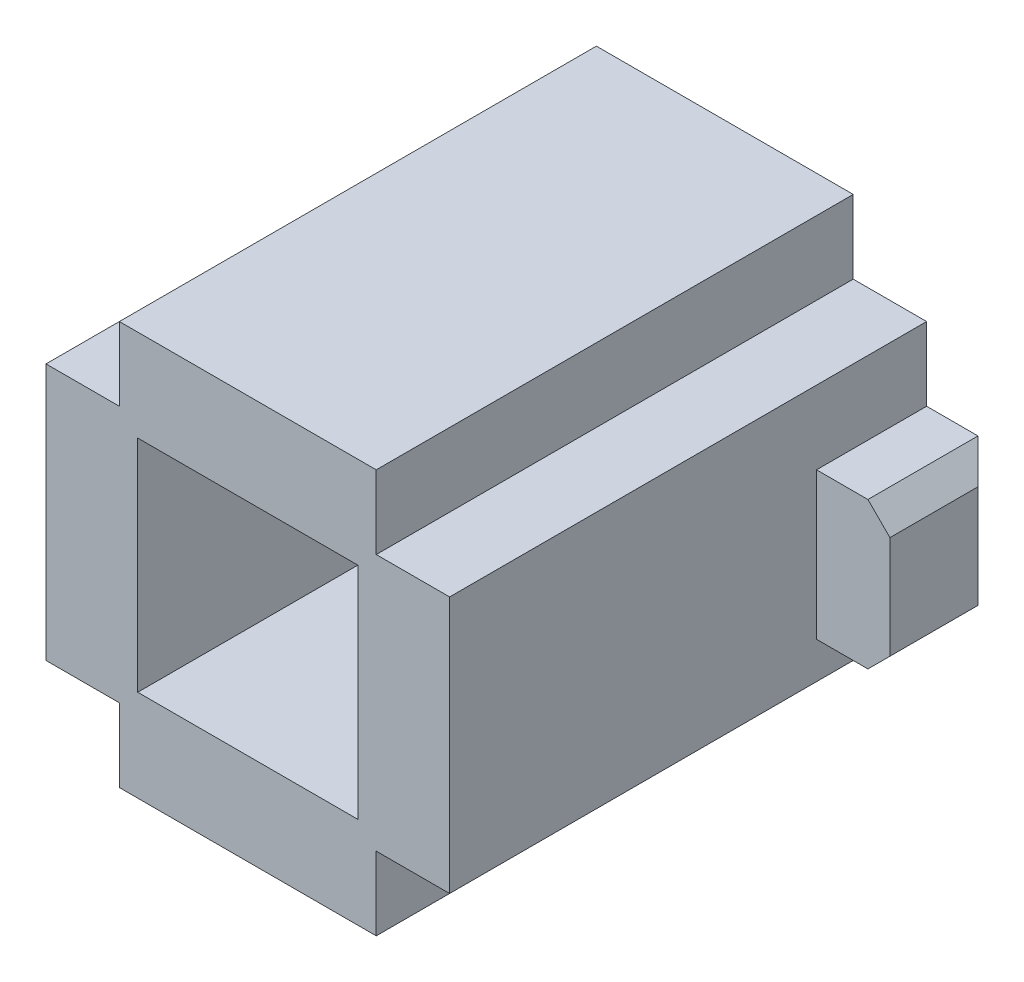
SolidWorks part; units mm, degrees
ref_plane "Front Plane" through (0, 0, 0) normal (0, 0, 1) x (1, 0, 0)
ref_plane "Top Plane" through (0, 0, 0) normal (0, 1, 0) x (1, 0, 0)
ref_plane "Right Plane" through (0, 0, 0) normal (1, 0, 0) x (0, 0, -1)
sketch "Sketch1" plane through (0, 0, 0) normal (0, 0, 1) x (1, 0, 0)
  line L0 (-17.5, 27.5) -> (-17.5, 17.5) construction
  line L1 (-17.5, 27.5) -> (17.5, 27.5)
  line L2 (-27.5, 17.5) -> (-27.5, -17.5)
  line L3 (-17.5, -27.5) -> (17.5, -27.5)
  line L4 (27.5, 17.5) -> (27.5, -17.5)
  line L5 (-17.5, 17.5) -> (-27.5, 17.5) construction
  line L6 (17.5, 27.5) -> (17.5, 17.5) construction
  line L7 (17.5, 17.5) -> (27.5, 17.5) construction
  line L8 (-17.5, -27.5) -> (-17.5, -17.5) construction
  line L9 (-17.5, -17.5) -> (-27.5, -17.5) construction
  line L10 (17.5, -27.5) -> (17.5, -17.5) construction
  line L11 (17.5, -17.5) -> (27.5, -17.5) construction
  line L12 (-17.5, 27.5) -> (-17.5, 17.5)
  line L13 (-15, 15) -> (15, 15)
  line L14 (-15, 15) -> (-15, -15)
  line L15 (-15, -15) -> (15, -15)
  line L16 (15, 15) -> (15, -15)
  line L17 (-17.5, 17.5) -> (-27.5, 17.5)
  line L18 (17.5, 27.5) -> (17.5, 17.5)
  line L19 (17.5, 17.5) -> (27.5, 17.5)
  line L20 (27.5, -17.5) -> (17.5, -17.5)
  line L21 (17.5, -17.5) -> (17.5, -27.5)
  line L22 (-27.5, -17.5) -> (-17.5, -17.5)
  line L23 (-17.5, -17.5) -> (-17.5, -27.5)
  dimension "D3" = 27.5
  dimension "D4" = 27.5
  dimension "D5" = 10
  dimension "D6" = 10
  dimension "D7" = 10
  dimension "D8" = 10
  dimension "D9" = 10
  dimension "D10" = 10
  dimension "D11" = 10
  dimension "D12" = 30
  dimension "D13" = 30
  dimension "D14" = 15
  dimension "D15" = 15
extrude "Boss-Extrude1" add sketch "Sketch1" along normal mid plane 65
sketch "Sketch2" plane through (27.5, 0, 0) normal (1, 0, 0) x (0, 0, -1)
  line L0 (32.5, -17.5) -> (32.5, 17.5) construction
  line L1 (32.5, 7.5) -> (17.5, 7.5)
  line L2 (32.5, 7.5) -> (32.5, -12.5)
  line L3 (32.5, -12.5) -> (17.5, -12.5)
  line L4 (17.5, 7.5) -> (17.5, -12.5)
  dimension "D1" = 15
  dimension "D2" = 20
  dimension "D3" = 7.5
extrude "Boss-Extrude2" add sketch "Sketch2" along normal blind 10
chamfer "Chamfer1" distance 3 angle 45 3 edges at (37.5, -12.5, -25) (37.5, -2.5, -32.5) (37.5, 7.5, -25)
